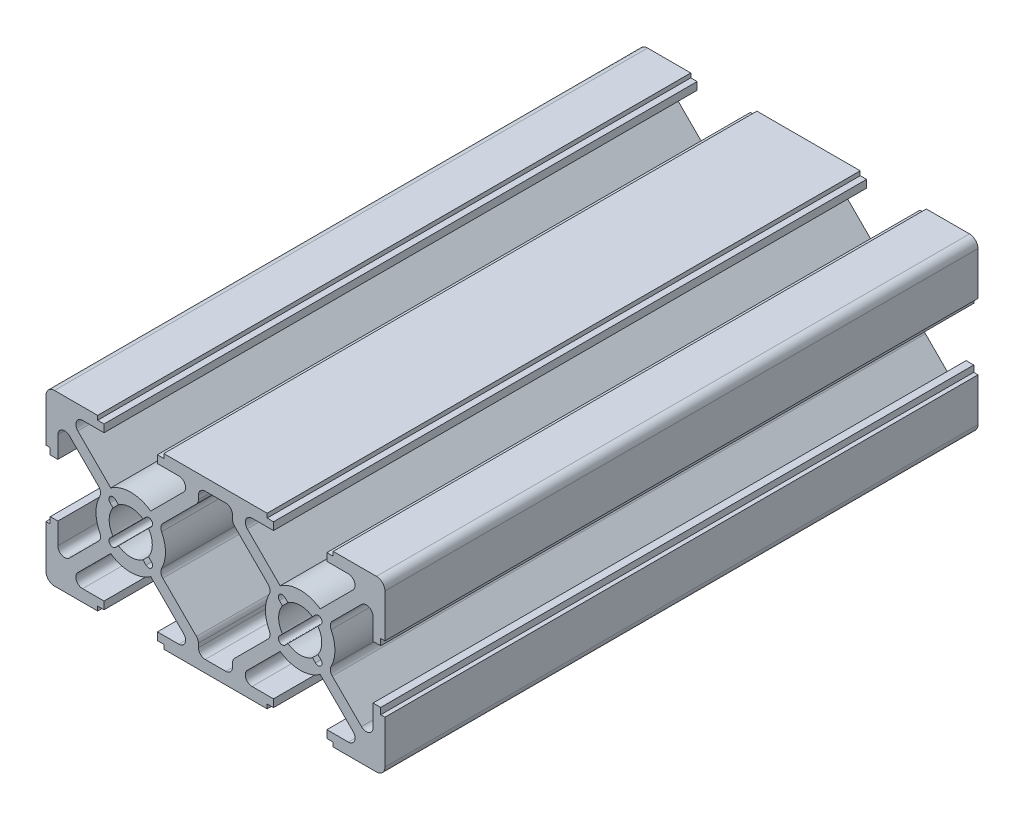
SolidWorks part; units mm, degrees
material "6063-T6"
ref_plane "Ön Düzlem" through (0, 0, 0) normal (0, 0, 1) x (1, 0, 0)
ref_plane "Üst Düzlem" through (0, 0, 0) normal (0, 1, 0) x (1, 0, 0)
ref_plane "Sağ Düzlem" through (0, 0, 0) normal (1, 0, 0) x (0, 0, -1)
sketch "Çizim3" plane through (0, 0, 0) normal (0, 0, 1) x (1, 0, 0)
  line L0 (20, 20) -> (20, 0) construction
  line L1 (0, 0) -> (40, 0) construction
  line L2 (1, 0) -> (6.1, 0)
  line L3 (0, 20) -> (40, 20) construction
  line L4 (40, 0) -> (40, 20) construction
  line L5 (26.1, 0) -> (26.1, 0.5)
  line L6 (0, 0) -> (20, 20) construction
  line L7 (20, 20) -> (40, 0) construction
  line L8 (0, 20) -> (20, 0) construction
  line L9 (20, 0) -> (40, 20) construction
  line L10 (0, 6.1) -> (0.5, 6.1)
  line L11 (0.5, 6.1) -> (0.5, 6.85)
  line L12 (0.5, 6.85) -> (1.4, 6.85)
  line L13 (1.4, 6.85) -> (1.4, 4.3213)
  line L14 (4.3213, 1.4) -> (6.85, 1.4)
  line L15 (6.85, 1.4) -> (6.85, 0.5)
  line L16 (6.85, 0.5) -> (6.1, 0.5)
  line L17 (6.1, 0.5) -> (6.1, 0)
  line L18 (0, 20) -> (0, 0) construction
  line L19 (0, 1) -> (0, 6.1)
  line L20 (6.85, 18.6) -> (6.85, 19.5)
  line L21 (6.85, 19.5) -> (6.1, 19.5)
  line L22 (1, 20) -> (6.1, 20)
  line L23 (4.3213, 18.6) -> (6.85, 18.6)
  line L24 (0, 19) -> (0, 13.9)
  line L25 (1.4, 13.15) -> (1.4, 15.6787)
  line L26 (0.5, 13.15) -> (1.4, 13.15)
  line L27 (0.5, 13.9) -> (0.5, 13.15)
  line L28 (0, 13.9) -> (0.5, 13.9)
  line L29 (6.1, 19.5) -> (6.1, 20)
  line L30 (70.8333, 107.5) -> (354.1667, 107.5) construction
  line L31 (2.7657, 16.2444) -> (6.6485, 12.3616)
  line L32 (3.7556, 17.2343) -> (7.6384, 13.3515)
  line L33 (3.7556, 2.7657) -> (7.6384, 6.6485)
  line L34 (2.7657, 3.7556) -> (6.6485, 7.6384)
  line L35 (0.495, 20.495) -> (20.495, 0.495) construction
  line L36 (-0.495, 19.505) -> (19.505, -0.495) construction
  line L37 (-0.495, 0.495) -> (19.505, 20.495) construction
  line L38 (0.495, -0.495) -> (20.495, 19.505) construction
  line L39 (26.1, 20) -> (13.9, 20)
  line L40 (13.9, 20) -> (13.9, 19.5)
  line L41 (13.9, 19.5) -> (13.15, 19.5)
  line L42 (13.15, 19.5) -> (13.15, 18.6)
  line L43 (13.15, 18.6) -> (15.6787, 18.6)
  line L44 (21.2103, 18.6) -> (18.7897, 18.6)
  line L45 (17.9897, 17.8) -> (17.9897, 17.3311)
  line L46 (26.1, 0) -> (13.9, 0)
  line L47 (13.9, 0) -> (13.9, 0.5)
  line L48 (13.9, 0.5) -> (13.15, 0.5)
  line L49 (13.15, 0.5) -> (13.15, 1.4)
  line L50 (13.15, 1.4) -> (15.6787, 1.4)
  line L51 (18.7897, 1.4) -> (21.2103, 1.4)
  line L52 (17.9897, 2.2) -> (17.9897, 2.6689)
  line L53 (8.2011, 12.4438) -> (8.5527, 12.0922)
  line L54 (7.5562, 11.7989) -> (7.9078, 11.4473)
  line L55 (12.3616, 13.3515) -> (16.2444, 17.2343)
  line L56 (13.3515, 12.3616) -> (17.7554, 16.7654)
  line L57 (7.5562, 8.2011) -> (7.9078, 8.5527)
  line L58 (8.2011, 7.5562) -> (8.5527, 7.9078)
  line L59 (12.3616, 6.6485) -> (16.2444, 2.7657)
  line L60 (13.3515, 7.6384) -> (17.7554, 3.2346)
  line L61 (26.1, 0.5) -> (26.85, 0.5)
  line L62 (12.0922, 8.5527) -> (12.4438, 8.2011)
  line L63 (11.4473, 12.0922) -> (11.7989, 12.4438)
  line L64 (12.0922, 11.4473) -> (12.4438, 11.7989)
  line L65 (11.4473, 7.9078) -> (11.7989, 7.5562)
  line L66 (26.85, 0.5) -> (26.85, 1.4)
  line L67 (26.85, 1.4) -> (24.3213, 1.4)
  line L68 (22.0103, 2.2) -> (22.0103, 2.6689)
  line L69 (26.6485, 7.6384) -> (22.2446, 3.2346)
  line L70 (27.6384, 6.6485) -> (23.7556, 2.7657)
  line L71 (36.2444, 2.7657) -> (32.3616, 6.6485)
  line L72 (37.2343, 3.7556) -> (33.3515, 7.6384)
  line L73 (35.6787, 1.4) -> (33.15, 1.4)
  line L74 (33.15, 1.4) -> (33.15, 0.5)
  line L75 (33.15, 0.5) -> (33.9, 0.5)
  line L76 (33.9, 0.5) -> (33.9, 0)
  line L77 (39, 0) -> (33.9, 0)
  line L78 (40, 1) -> (40, 6.1)
  line L79 (38.6, 6.85) -> (38.6, 4.3213)
  line L80 (39.5, 6.85) -> (38.6, 6.85)
  line L81 (39.5, 6.1) -> (39.5, 6.85)
  line L82 (40, 6.1) -> (39.5, 6.1)
  line L83 (26.1, 20) -> (26.1, 19.5)
  line L84 (26.1, 19.5) -> (26.85, 19.5)
  line L85 (26.85, 19.5) -> (26.85, 18.6)
  line L86 (26.85, 18.6) -> (24.3213, 18.6)
  line L87 (26.6485, 12.3616) -> (22.2446, 16.7654)
  line L88 (27.6384, 13.3515) -> (23.7556, 17.2343)
  line L89 (22.0103, 17.8) -> (22.0103, 17.3311)
  line L90 (27.9078, 11.4473) -> (27.5562, 11.7989)
  line L91 (27.9078, 8.5527) -> (27.5562, 8.2011)
  line L92 (28.5527, 7.9078) -> (28.2011, 7.5562)
  line L93 (31.7989, 7.5562) -> (31.4473, 7.9078)
  line L94 (32.4438, 8.2011) -> (32.0922, 8.5527)
  line L95 (32.4438, 11.7989) -> (32.0922, 11.4473)
  line L96 (31.7989, 12.4438) -> (31.4473, 12.0922)
  line L97 (36.2444, 17.2343) -> (32.3616, 13.3515)
  line L98 (35.6787, 18.6) -> (33.15, 18.6)
  line L99 (33.15, 18.6) -> (33.15, 19.5)
  line L100 (33.15, 19.5) -> (33.9, 19.5)
  line L101 (33.9, 19.5) -> (33.9, 20)
  line L102 (37.2343, 16.2444) -> (33.3515, 12.3616)
  line L103 (38.6, 13.15) -> (38.6, 15.6787)
  line L104 (39.5, 13.15) -> (38.6, 13.15)
  line L105 (39.5, 13.9) -> (39.5, 13.15)
  line L106 (40, 13.9) -> (39.5, 13.9)
  line L107 (40, 19) -> (40, 13.9)
  line L108 (39, 20) -> (33.9, 20)
  line L109 (28.5527, 12.0922) -> (28.2011, 12.4438)
  arc A0 (7.9078, 11.4473) -> (7.9078, 8.5527) centre (10, 10) ccw
  arc A1 (2.7657, 16.2444) -> (1.4, 15.6787) centre (2.2, 15.6787) ccw
  arc A2 (3.7556, 2.7657) -> (4.3213, 1.4) centre (4.3213, 2.2) ccw
  arc A3 (2.7657, 3.7556) -> (1.4, 4.3213) centre (2.2, 4.3213) cw
  arc A4 (3.7556, 17.2343) -> (4.3213, 18.6) centre (4.3213, 17.8) cw
  arc A5 (15.6787, 18.6) -> (16.2444, 17.2343) centre (15.6787, 17.8) cw
  arc A6 (18.7897, 18.6) -> (17.9897, 17.8) centre (18.7897, 17.8) ccw
  arc A7 (17.9897, 17.3311) -> (17.7554, 16.7654) centre (17.1897, 17.3311) cw
  arc A8 (15.6787, 1.4) -> (16.2444, 2.7657) centre (15.6787, 2.2) ccw
  arc A9 (18.7897, 1.4) -> (17.9897, 2.2) centre (18.7897, 2.2) cw
  arc A10 (17.9897, 2.6689) -> (17.7554, 3.2346) centre (17.1897, 2.6689) ccw
  arc A11 (6.6485, 12.3616) -> (6.6485, 7.6384) centre (10, 10) ccw
  arc A12 (12.3616, 13.3515) -> (7.6384, 13.3515) centre (10, 10) ccw
  arc A13 (7.6384, 6.6485) -> (12.3616, 6.6485) centre (10, 10) ccw
  arc A14 (13.3515, 7.6384) -> (13.3515, 12.3616) centre (10, 10) ccw
  arc A15 (11.4473, 12.0922) -> (8.5527, 12.0922) centre (10, 10) ccw
  arc A16 (8.2011, 12.4438) -> (7.5562, 11.7989) centre (7.8787, 12.1213) ccw
  arc A17 (12.4438, 11.7989) -> (11.7989, 12.4438) centre (12.1213, 12.1213) ccw
  arc A18 (11.7989, 7.5562) -> (12.4438, 8.2011) centre (12.1213, 7.8787) ccw
  arc A19 (7.5562, 8.2011) -> (8.2011, 7.5562) centre (7.8787, 7.8787) ccw
  arc A20 (8.5527, 7.9078) -> (11.4473, 7.9078) centre (10, 10) ccw
  arc A21 (12.0922, 8.5527) -> (12.0922, 11.4473) centre (10, 10) ccw
  arc A22 (21.2103, 1.4) -> (22.0103, 2.2) centre (21.2103, 2.2) ccw
  arc A23 (24.3213, 1.4) -> (23.7556, 2.7657) centre (24.3213, 2.2) cw
  arc A24 (22.0103, 2.6689) -> (22.2446, 3.2346) centre (22.8103, 2.6689) cw
  arc A25 (32.3616, 6.6485) -> (27.6384, 6.6485) centre (30, 10) cw
  arc A26 (37.2343, 3.7556) -> (38.6, 4.3213) centre (37.8, 4.3213) ccw
  arc A27 (36.2444, 2.7657) -> (35.6787, 1.4) centre (35.6787, 2.2) cw
  arc A28 (26.6485, 7.6384) -> (26.6485, 12.3616) centre (30, 10) cw
  arc A29 (21.2103, 18.6) -> (22.0103, 17.8) centre (21.2103, 17.8) cw
  arc A30 (24.3213, 18.6) -> (23.7556, 17.2343) centre (24.3213, 17.8) ccw
  arc A31 (22.0103, 17.3311) -> (22.2446, 16.7654) centre (22.8103, 17.3311) ccw
  arc A32 (28.5527, 12.0922) -> (31.4473, 12.0922) centre (30, 10) cw
  arc A33 (27.5562, 11.7989) -> (28.2011, 12.4438) centre (27.8787, 12.1213) cw
  arc A34 (27.9078, 8.5527) -> (27.9078, 11.4473) centre (30, 10) cw
  arc A35 (31.4473, 7.9078) -> (28.5527, 7.9078) centre (30, 10) cw
  arc A36 (32.4438, 8.2011) -> (31.7989, 7.5562) centre (32.1213, 7.8787) cw
  arc A37 (32.0922, 11.4473) -> (32.0922, 8.5527) centre (30, 10) cw
  arc A38 (31.7989, 12.4438) -> (32.4438, 11.7989) centre (32.1213, 12.1213) cw
  arc A39 (33.3515, 12.3616) -> (33.3515, 7.6384) centre (30, 10) cw
  arc A40 (27.6384, 13.3515) -> (32.3616, 13.3515) centre (30, 10) cw
  arc A41 (36.2444, 17.2343) -> (35.6787, 18.6) centre (35.6787, 17.8) ccw
  arc A42 (37.2343, 16.2444) -> (38.6, 15.6787) centre (37.8, 15.6787) cw
  arc A43 (39, 0) -> (40, 1) centre (39, 1) ccw
  arc A44 (40, 19) -> (39, 20) centre (39, 19) ccw
  arc A45 (0, 1) -> (1, 0) centre (1, 1) ccw
  arc A46 (0, 19) -> (1, 20) centre (1, 19) cw
  arc A48 (28.2011, 7.5562) -> (27.5562, 8.2011) centre (27.8787, 7.8787) cw
  point P10 (20, 10)
  point P109 (20, 1.4)
  point P145 (20, 18.6)
  point P197 (0, 0)
  dimension "D10" = 0.8
  dimension "D11" = 0.8
  dimension "D13" = 0.8
  dimension "D14" = 0.8
  dimension "D16" = 0.8
  dimension "D17" = 0.8
  dimension "D18" = 20
  dimension "D20" = 1
  dimension "D1" = 6.3
  dimension "D2" = 20
  dimension "D3" = 6.1
  dimension "D4" = 0.5
  dimension "D5" = 1.4
  dimension "D6" = 0.7
  dimension "D12" = 6.3
  dimension "D15" = 6.3
  dimension "D19" = 10
  dimension "D7" = 0.7
  dimension "D8" = 0.7
  dimension "D9" = 0.7
extrude "Yükseklik-Ekstrüzyon2" add sketch "Çizim3" along normal blind 70 contours L22 L29 L21 L20 L23 A4 L32 A12 L55 A5 L43 L42 L41 L40 L39 L83 L84 L85 L86 A30 L88 A40 L97 A41 L98 L99 L100 L101 L108 A44 L107 L106 L105 L104 L103 A42 L102 A39 L72 A26 L79 L80 L81 L82 L78 A43 L77 L76 L75 L74 L73 A27 L71 A25 L70 A23 L67 L66 L61 L5 L46 L47 L48 L49 L50 A8 L59 A13 L33 A2 L14 L15 L16 L17 L2 A45 L19 L10 L11 L12 L13 A3 L34 A11 L31 A1 L25 L26 L27 L28 L24 A46
fillet "Radyus1" radius 0.8 8 edges at (26.6485, 7.6384, 35) (26.6485, 12.3616, 35) (33.3515, 7.6384, 35) (33.3515, 12.3616, 35) (13.3515, 12.3616, 35) (13.3515, 7.6384, 35) (6.6485, 7.6384, 35) (6.6485, 12.3616, 35)
